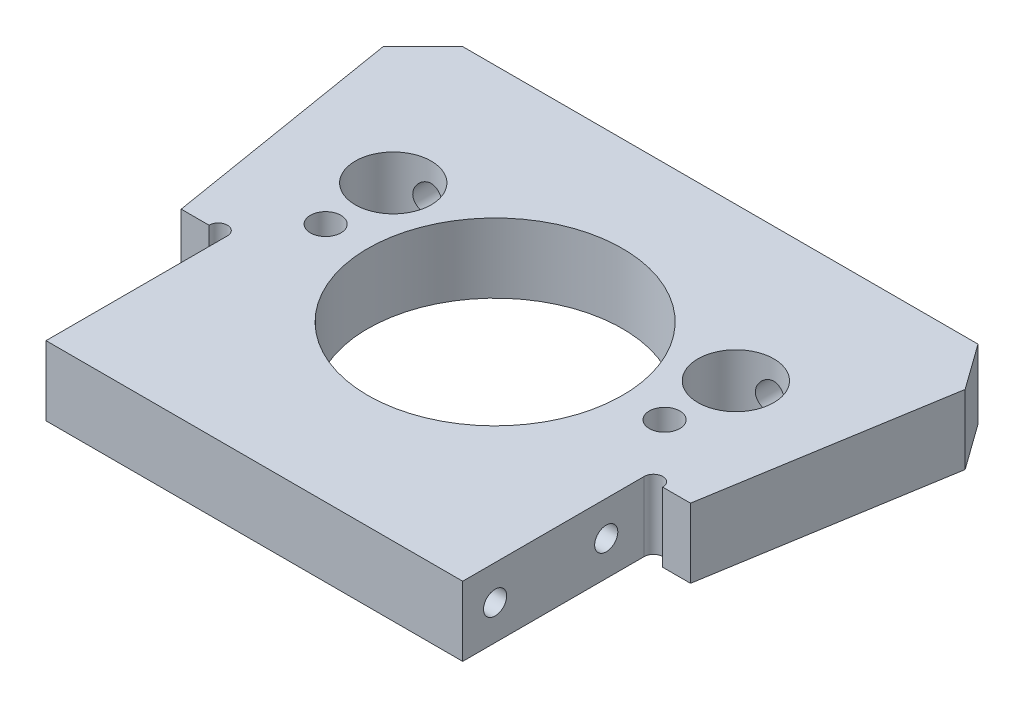
SolidWorks part; units mm, degrees
material "7075-T6 (SN)"
ref_plane "Front Plane" through (0, 0, 0) normal (0, 0, 1) x (1, 0, 0)
ref_plane "Top Plane" through (0, 0, 0) normal (0, 1, 0) x (1, 0, 0)
ref_plane "Right Plane" through (0, 0, 0) normal (1, 0, 0) x (0, 0, -1)
sketch "Sketch1" plane through (0, 0, 0) normal (0, 1, 0) x (1, 0, 0)
  line L0 (-22.5, 0) -> (22.5, 0)
  line L1 (22.5, 0) -> (22.5, 14.6)
  line L2 (22.5, 14.6) -> (27.5, 14.6)
  line L4 (32.5, 45) -> (-32.5, 45)
  line L6 (-27.5, 14.6) -> (-22.5, 14.6)
  line L7 (-22.5, 14.6) -> (-22.5, 0)
  line L8 (27.5, 14.6) -> (32.5, 45)
  line L9 (-27.5, 14.6) -> (-32.5, 45)
  point P8 (0, 45)
  dimension "D1" = 45
  dimension "D2" = 45
  dimension "D3" = 14.6
  dimension "D4" = 5
  dimension "D5" = 65
extrude "Boss-Extrude1" add sketch "Sketch1" along normal blind 7.5
sketch "Sketch2" plane through (0, 7.5, 0) normal (0, 1, 0) x (1, 0, 0)
  line L0 (-27.5, 14.6) -> (-22.5, 14.6) construction
  line L5 (22.5, 14.6) -> (27.5, 14.6) construction
  circle A4 centre (-23.5, 14.6) radius 1
  circle A5 centre (23.5, 14.6) radius 1
  dimension "D1" = 2
extrude "Cut-Extrude1" cut sketch "Sketch2" against normal up to next and the other way through all
chamfer "Chamfer1" distance 5 angle 45 2 edges at (-32.5, 3.75, -45) (32.5, 3.75, -45)
sketch "Sketch3" plane through (0, 7.5, 0) normal (0, 1, 0) x (1, 0, 0)
  line L0 (-22.5, 0) -> (22.5, 0) construction
  circle A0 centre (0, 21) radius 13.75
  dimension "D2" = 27.5
  dimension "D1" = 21
extrude "Cut-Extrude2" cut sketch "Sketch3" against normal up to next
sketch "Sketch11" plane through (0, 0, 0) normal (0, 0, 1) x (1, 0, 0)
  line L4 (-22.5, 0) -> (22.5, 0)
  line L5 (22.5, 0) -> (22.5, 7.5)
  line L6 (22.5, 7.5) -> (-22.5, 7.5)
  line L7 (-22.5, 7.5) -> (-22.5, 0)
  line L8 (-22.5, 0) -> (22.5, 0)
  line L9 (22.5, 0) -> (22.5, 7.5)
  line L10 (22.5, 7.5) -> (-22.5, 7.5)
  line L11 (-22.5, 7.5) -> (-22.5, 0)
  dimension "D1" = 0
extrude "Boss-Extrude2" add sketch "Sketch11" along normal blind 5
hole_wizard "M4 Tapped Hole1" positions "Sketch4" profile "Sketch5" tap size "M4" standard "DIN" end condition up to next
sketch "Sketch4" plane through (0, 0, 0) normal (0, -1, 0) x (-1, 0, 0)
  point P0 (-18.3, 21)
  point P2 (18.3, 21)
  dimension "D1" = 21
  dimension "D2" = 18.3
  dimension "D3" = 18.3
sketch "Sketch5" plane through (18.3, 0, -21) normal (1, 0, 0) x (0, 0, -1)
  line L0 (0, 0) -> (0, 7.5)
  line L1 (0, 7.5) -> (1.65, 7.5)
  line L2 (1.65, 7.5) -> (1.65, 0)
  line L5 (1.65, 0) -> (0, 0)
  line L11 (0, -6.35) -> (0, 107.95) construction
  dimension "Thru Tap Drill Dia." = 3.3
  dimension "Thru Tap Drill Depth" = 7.5
cosmetic thread "Hole Thread1" parameters "D2"=4
cosmetic thread "Hole Thread2" parameters "D2"=4
sketch "Sketch6" plane through (0, 0, 0) normal (0, -1, 0) x (1, 0, 0)
  circle A0 centre (18.5, -28.5) radius 4.1
  circle A1 centre (-18.5, -28.5) radius 4.1
  circle A2 centre (0, -21) radius 13.75 construction
  dimension "D1" = 18.5
  dimension "D2" = 8.2
  dimension "D4" = 7.5
  dimension "D3" = 18.5
extrude "Cut-Extrude3" cut sketch "Sketch6" against normal up to next
hole_wizard "M4 Tapped Hole2" positions "Sketch7" profile "Sketch8" tap size "M4" standard "DIN"
sketch "Sketch7" plane through (0, 0, -45) normal (0, 0, -1) x (-1, 0, 0)
  line L0 (-28.1485, 7.5) -> (27.5, 7.5) construction
  point P0 (-18.5, 3.75)
  point P2 (18.5, 3.75)
  dimension "D1" = 3.75
  dimension "D2" = 18.5
  dimension "D3" = 18.5
sketch "Sketch8" plane through (18.5, 3.75, -45) normal (1, 0, 0) x (0, 1, 0)
  line L0 (0, 0) -> (0, 12.4)
  line L1 (0, 12.4) -> (1.65, 12.4)
  line L2 (1.65, 12.4) -> (1.65, 0)
  line L5 (1.65, 0) -> (0, 0)
  line L11 (0, -6.35) -> (0, 107.95) construction
  dimension "Thru Tap Drill Dia." = 3.3
  dimension "Thru Tap Drill Depth" = 12.4
cosmetic thread "Hole Thread3" parameters "D2"=4
cosmetic thread "Hole Thread4" parameters "D2"=4
hole_wizard "M3 Tapped Hole1" positions "Sketch9" profile "Sketch10" tap size "M3" standard "DIN"
sketch "Sketch9" plane through (22.5, 0, 0) normal (1, 0, 0) x (0, 0, -1)
  line L0 (-5, 0) -> (14.6, 0) construction
  line L4 (-5, 0) -> (-5, 7.5) construction
  point P0 (10.5, 3.75)
  point P2 (-1.5, 3.75)
  dimension "D1" = 3.75
  dimension "D2" = 12
  dimension "D3" = 3.5
sketch "Sketch10" plane through (22.5, 3.75, -10.5) normal (0, 1, 0) x (0, 0, -1)
  line L0 (0, 0) -> (0, 10.7511)
  line L1 (0, 10.7511) -> (1.25, 10)
  line L2 (1.25, 10) -> (1.25, 0)
  line L5 (1.25, 0) -> (0, 0)
  line L10 (0, 10.7511) -> (-1.25, 10) construction
  line L11 (0, -6.35) -> (0, 107.95) construction
  dimension "Tap Drill Dia." = 2.5
  dimension "Tap Drill Depth" = 10
  dimension "Drill Angle" = 118
cosmetic thread "Hole Thread5" parameters "D1"=6, "D2"=3
cosmetic thread "Hole Thread6" parameters "D1"=6, "D2"=3
mirror "Mirror1" about plane through (0, 0, 0) normal (1, 0, 0) of "M3 Tapped Hole1"
